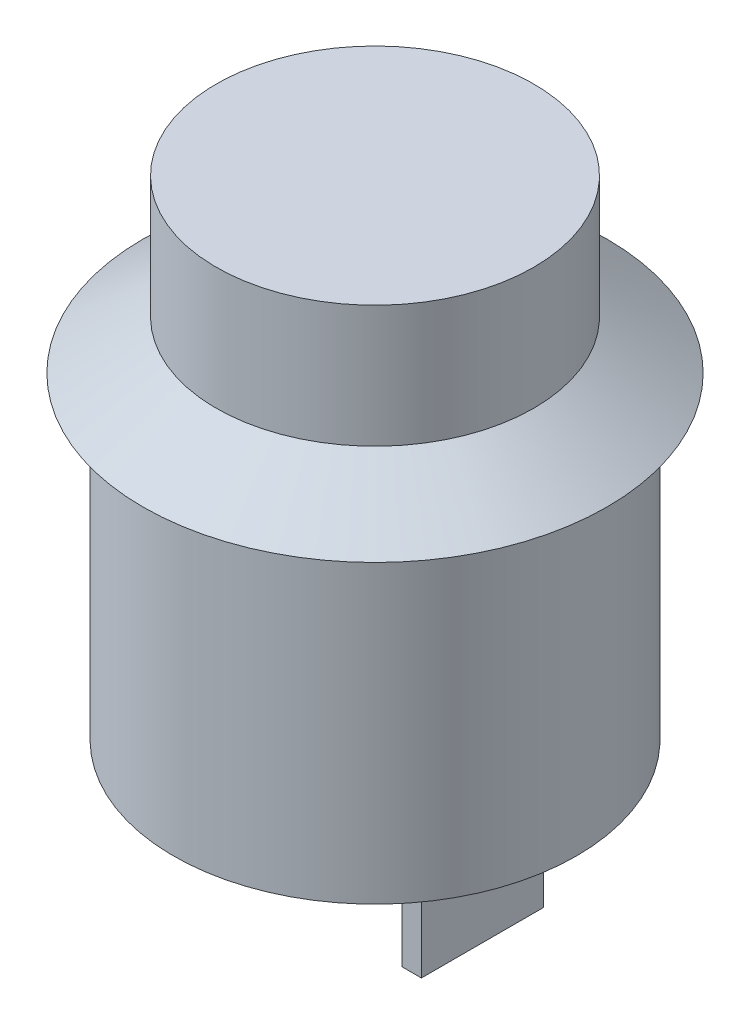
SolidWorks part; units mm, degrees
ref_plane "Спереди" through (0, 0, 0) normal (0, 0, 1) x (1, 0, 0)
ref_plane "Сверху" through (0, 0, 0) normal (0, 1, 0) x (1, 0, 0)
ref_plane "Справа" through (0, 0, 0) normal (1, 0, 0) x (0, 0, -1)
sketch "Эскиз1" plane through (0, 0, 0) normal (0, 0, 1) x (1, 0, 0)
  line L0 (0, -275.0096) -> (0, 13475.4694) construction
  line L1 (0, 0) -> (8.25, 0)
  line L2 (8.25, 0) -> (8.25, 13)
  line L3 (8.25, 13) -> (9.5, 13)
  line L4 (9.5, 13) -> (6.5, 15)
  line L5 (6.5, 15) -> (6.5, 20)
  line L6 (6.5, 20) -> (0, 20)
  line L7 (0, 20) -> (0, 0)
  point P8 (6.5, 17.5)
  dimension "D1" = 13
  dimension "D2" = 5
  dimension "D3" = 19
  dimension "D4" = 16.5
  dimension "D5" = 2
  dimension "D6" = 20
revolve "Повернуть1" add sketch "Эскиз1" angle 360 about L0
sketch "Эскиз2" plane through (0, 0, 0) normal (0, -1, 0) x (1, 0, 0)
  line L0 (-4, 0) -> (4, 0) construction
  line L2 (-4.4, 2.5) -> (-3.6, 2.5)
  line L3 (-4.4, 2.5) -> (-4.4, -2.5)
  line L4 (-4.4, -2.5) -> (-3.6, -2.5)
  line L5 (-3.6, 2.5) -> (-3.6, -2.5)
  line L6 (-4.4, 2.5) -> (-3.6, -2.5) construction
  line L7 (-4.4, -2.5) -> (-3.6, 2.5) construction
  line L8 (3.6, 2.5) -> (4.4, 2.5)
  line L9 (3.6, 2.5) -> (3.6, -2.5)
  line L10 (3.6, -2.5) -> (4.4, -2.5)
  line L11 (4.4, 2.5) -> (4.4, -2.5)
  line L12 (3.6, 2.5) -> (4.4, -2.5) construction
  line L13 (3.6, -2.5) -> (4.4, 2.5) construction
  point P3 (0, 0)
  dimension "D1" = 8
  dimension "D2" = 0.8
  dimension "D3" = 5
extrude "Бобышка-Вытянуть1" add sketch "Эскиз2" along normal blind 5
